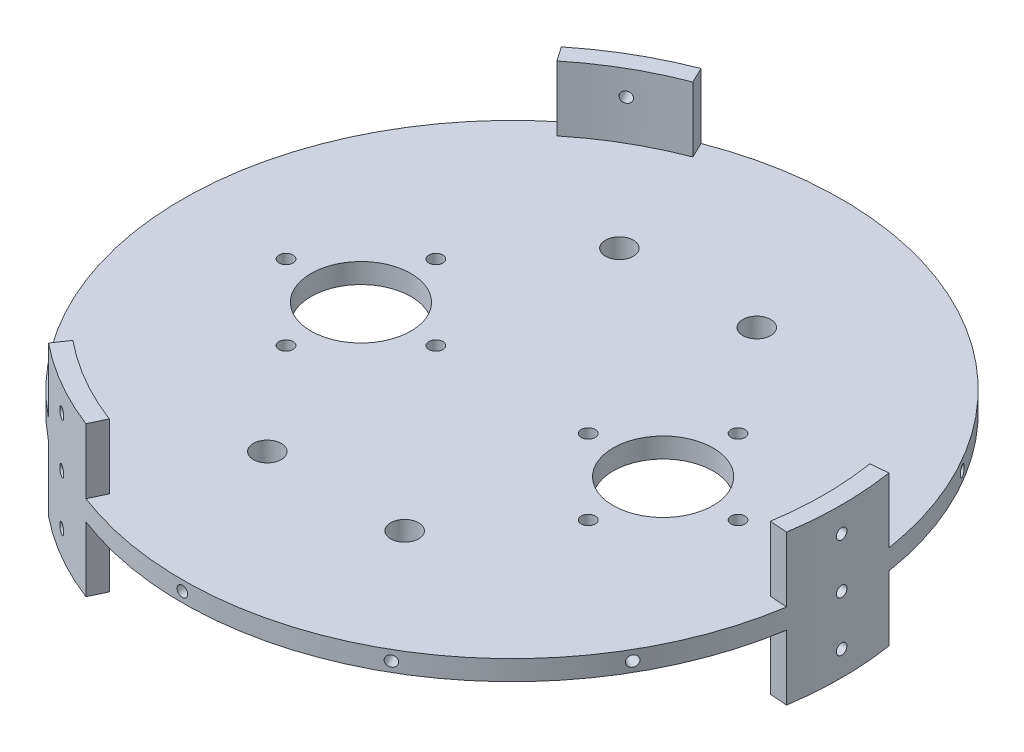
SolidWorks part; units mm, degrees
material "6061-T6 (SS)"
ref_plane "Front" through (0, 0, 0) normal (0, 0, 1) x (1, 0, 0)
ref_plane "Top" through (0, 0, 0) normal (0, 1, 0) x (1, 0, 0)
ref_plane "Right" through (0, 0, 0) normal (1, 0, 0) x (0, 0, -1)
sketch "Sketch1" plane through (0, 0, 0) normal (0, 1, 0) x (1, 0, 0)
  line L1 (0, 0) -> (127.635, 0)
  line L2 (0, 0) -> (0, 127.635)
  line L3 (0, 127.635) -> (127.635, 127.635)
  line L4 (127.635, 0) -> (127.635, 127.635)
  dimension "D1" = 127.635
  dimension "D2" = 127.635
extrude "Main Plate" add sketch "Sketch1" along normal blind 12.7
sketch "Sketch9" plane through (0, 12.7, 0) normal (0, 1, 0) x (1, 0, 0)
  circle A0 centre (63.8175, 63.8175) radius 85.725
  dimension "D1" = 171.45
extrude "Boss-Extrude1" add sketch "Sketch9" against normal up to surface (12.7 mm away) contours A0 up to face at (63.8175, 0, -63.8175)
sketch "Sketch10" plane through (0, 12.7, 0) normal (0, 1, 0) x (1, 0, 0)
  circle A0 centre (63.8175, 63.8175) radius 97.0396
  circle A1 centre (63.8175, 63.8175) radius 83.82
extrude "Cut-Extrude1" cut sketch "Sketch10" against normal blind 167.64 contours A0 | A1
sketch "Sketch14" plane through (0, 12.7, 0) normal (0, 1, 0) x (1, 0, 0)
  line L0 (201.1692, 63.8175) -> (-73.4523, 63.8175) construction
ref_plane "Plane1" through (0, 0, -63.8175) normal (0, 0, -1) x (-1, 0, 0)
ref_plane "Plane3" through (0, 6.35, 0) normal (0, 1, 0) x (1, 0, 0)
ref_plane "Plane2" through (-20.0025, 0, 0) normal (-1, 0, 0) x (0, 0, 1)
sketch "Sketch18" plane through (0, 6.35, 0) normal (0, 1, 0) x (1, 0, 0)
  circle A0 centre (63.8175, 63.8175) radius 83.82
  circle A1 centre (63.8175, 63.8175) radius 79.375
  dimension "D1" = 158.75
extrude "Boss-Extrude2" add sketch "Sketch18" along normal mid plane 38.1
sketch "Sketch15" plane through (-20.0025, 0, 0) normal (-1, 0, 0) x (0, 0, 1)
  line L0 (-63.8175, 87.3125) -> (-63.8175, -87.3125) construction
  line L1 (20.0025, 12.7) -> (-147.6375, 12.7) construction
  line L2 (-147.6375, -12.7) -> (20.0025, -12.7) construction
  line L3 (15.5575, 25.4) -> (-143.1925, 25.4) construction
  circle A0 centre (-63.8175, 6.35) radius 1.3526
  circle A1 centre (-63.8175, 19.05) radius 1.3525
  circle A2 centre (-63.8175, -6.35) radius 1.3526
  dimension "D1" = 2.7051
  dimension "D2" = 6.35
  dimension "D3" = 2.7051
  dimension "D4" = 2.7051
  dimension "D5" = 6.35
  dimension "D6" = 6.35
extrude "Cut-Extrude3" cut sketch "Sketch15" against normal blind 15.24
pattern_circular "CirPattern1" count 12 over 360 about axis through (63.8175, 0, -63.8175) along (0, 1, 0) of "Cut-Extrude3"
sketch "Sketch20" plane through (0, 12.7, 0) normal (0, 1, 0) x (1, 0, 0)
  line L0 (63.8175, 143.1925) -> (63.8175, -15.5575) construction
  line L1 (-15.5575, 63.8175) -> (143.1925, 63.8175) construction
  circle A0 centre (63.8175, 63.8175) radius 79.375 construction
ref_plane "Plane4" through (63.8175, 0, 0) normal (-1, 0, 0) x (0, 0, 1)
sketch "Sketch21" plane through (0, 12.7, 0) normal (0, 1, 0) x (1, 0, 0)
  line L1 (-15.5575, 63.8175) -> (143.1925, 63.8175) construction
  line L2 (102.235, 63.8175) -> (102.235, 100.651) construction
  line L3 (63.8175, 87.3125) -> (63.8175, -87.3125) construction
  circle A0 centre (102.235, 63.8175) radius 12.7
  circle A1 centre (102.235, 82.8675) radius 1.778
  circle A2 centre (25.4, 63.8175) radius 12.7
  circle A3 centre (121.285, 63.8175) radius 1.778
  circle A4 centre (102.235, 44.7675) radius 1.778
  circle A5 centre (83.185, 63.8175) radius 1.778
  circle A6 centre (25.4, 82.8675) radius 1.778
  circle A7 centre (6.35, 63.8175) radius 1.778
  circle A8 centre (25.4, 44.7675) radius 1.778
  circle A9 centre (44.45, 63.8175) radius 1.778
  dimension "D1" = 25.4
  dimension "D2" = 3.556
  dimension "D6" = 19.05
  dimension "D3" = 19.05
  dimension "D4" = 76.835
  dimension "D7" = 19.05
  dimension "D5" = 4
extrude "CO2 Mounts" cut sketch "Sketch21" against normal through all
sketch "Sketch22" plane through (0, 12.7, 0) normal (0, 1, 0) x (1, 0, 0)
  line L0 (63.8175, 87.3125) -> (63.8175, -87.3125) construction
  line L1 (87.3125, 63.8175) -> (-87.3125, 63.8175) construction
  circle A0 centre (46.355, 108.585) radius 3.556
  circle A1 centre (81.28, 108.585) radius 3.556
  circle A2 centre (81.28, 19.05) radius 3.556
  circle A3 centre (46.355, 19.05) radius 3.556
  dimension "D1" = 7.112
  dimension "D2" = 34.925
  dimension "D3" = 89.535
extrude "Cut-Extrude5" cut sketch "Sketch22" against normal through all
sketch "Sketch23" plane through (0, 12.7, 0) normal (0, 1, 0) x (1, 0, 0)
  line L0 (13.6787, 125.352) -> (7.5523, 134.2379)
  line L1 (15.1867, 11.8815) -> (13.6787, 2.283) construction
  line L3 (-15.5575, 63.8175) -> (143.1925, 63.8175) construction
  line L4 (63.8175, 143.1925) -> (63.8175, -15.5575) construction
  line L5 (-15.5575, 63.8175) -> (143.1925, 63.8175)
  line L6 (63.8175, 143.1925) -> (63.8175, -15.5575)
  line L7 (13.6787, 2.283) -> (6.9592, -7.4631)
  line L8 (-19.2671, 125.3206) -> (-48.797, 60.3978)
  line L9 (-48.797, 60.3978) -> (-9.8843, 7.0525)
  line L10 (-9.8843, 7.0525) -> (6.9592, -7.4631)
  line L11 (24.1345, -4.9259) -> (13.6787, 2.283) construction
  line L14 (7.5523, 134.2379) -> (-19.2671, 125.3206)
  line L15 (24.1345, 132.5609) -> (13.6787, 125.352) construction
  line L28 (63.8175, 63.8175) -> (24.1345, -4.9259) construction
  line L29 (63.8175, 63.8175) -> (24.1345, 132.5609) construction
  line L30 (142.1773, 76.4717) -> (152.9359, 77.3344)
  line L31 (152.9359, 77.3344) -> (158.6231, 105.0193)
  line L32 (158.6231, 105.0193) -> (117.1632, 163.0543)
  line L33 (117.1632, 163.0543) -> (51.5085, 156.0277)
  line L34 (51.5085, 156.0277) -> (30.5159, 148.6985)
  line L35 (35.5964, 138.0062) -> (30.5159, 148.6985)
  line L36 (35.5964, -10.3712) -> (30.9643, -20.1198)
  line L37 (30.9643, -20.1198) -> (52.0965, -38.8874)
  line L38 (52.0965, -38.8874) -> (123.0863, -31.9996)
  line L39 (123.0863, -31.9996) -> (149.8284, 28.3723)
  line L40 (149.8284, 28.3723) -> (153.9775, 50.217)
  line L41 (142.1773, 51.1633) -> (153.9775, 50.217)
  circle A0 centre (63.8175, 63.8175) radius 79.375 construction
  arc A1 (13.6787, 2.283) -> (13.6787, 125.352) centre (63.8175, 63.8175) cw
  circle A3 centre (63.8175, 63.8175) radius 79.375
  circle A4 centre (63.8175, 63.8175) radius 79.375
  arc A6 (35.5964, 138.0062) -> (142.1773, 76.4717) centre (63.8175, 63.8175) cw
  arc A7 (142.1773, 51.1633) -> (35.5964, -10.3712) centre (63.8175, 63.8175) cw
  dimension "D1" = 79.375
  dimension "D2" = 0
  dimension "D3" = 12.7
  dimension "D4" = 90
  dimension "D5" = 12.7
  dimension "D6" = 90
  dimension "D8" = 60.004
  dimension "D9" = 60.004
  dimension "D7" = 3
extrude "Cut-Extrude6" cut sketch "Sketch23" along normal up to next (12.7 mm away)
mirror "Mirror1" about plane through (0, 6.35, 0) normal (0, 1, 0) of "Cut-Extrude6"
sketch "Sketch25" plane through (0, 0, 0) normal (0, -1, 0) x (1, 0, 0)
  line L0 (-15.5575, -63.8175) -> (143.1925, -63.8175) construction
  line L1 (63.8175, -143.1925) -> (63.8175, 15.5575) construction
  line L2 (-15.5575, -63.8175) -> (143.1925, -63.8175)
  line L3 (63.8175, -143.1925) -> (63.8175, 15.5575)
  line L4 (63.8175, -143.1925) -> (63.8175, 15.5575)
  line L5 (-15.5575, -63.8175) -> (143.1925, -63.8175)
  line L6 (35.5964, -138.0062) -> (33.6829, -142.0332) construction
  line L7 (13.6787, -125.352) -> (11.148, -129.0227) construction
  line L8 (142.1773, -51.1633) -> (146.6216, -50.8069) construction
  line L9 (146.6216, -76.8281) -> (142.1773, -76.4717) construction
  line L10 (33.6829, 14.3982) -> (35.5964, 10.3712) construction
  line L11 (11.148, 1.3877) -> (13.6787, -2.283) construction
  line L12 (35.5964, -138.0062) -> (33.6829, -142.0332)
  line L13 (13.6787, -125.352) -> (11.148, -129.0227)
  line L14 (142.1773, -51.1633) -> (146.6216, -50.8069)
  line L15 (146.6216, -76.8281) -> (142.1773, -76.4717)
  line L16 (33.6829, 14.3982) -> (35.5964, 10.3712)
  line L17 (11.148, 1.3877) -> (13.6787, -2.283)
  circle A0 centre (46.355, -19.05) radius 6.35
  circle A1 centre (81.28, -19.05) radius 6.35
  circle A2 centre (81.28, -108.585) radius 6.35
  circle A3 centre (46.355, -108.585) radius 6.35
  arc A4 (13.6787, -125.352) -> (35.5964, -138.0062) centre (63.8175, -63.8175) ccw construction
  arc A5 (142.1773, -76.4717) -> (142.1773, -51.1633) centre (63.8175, -63.8175) ccw construction
  arc A6 (35.5964, 10.3712) -> (13.6787, -2.283) centre (63.8175, -63.8175) ccw construction
  arc A7 (146.6216, -50.8069) -> (33.6829, 14.3982) centre (63.8175, -63.8175) ccw construction
  arc A8 (33.6829, -142.0332) -> (146.6216, -76.8281) centre (63.8175, -63.8175) ccw construction
  arc A9 (11.148, 1.3877) -> (11.148, -129.0227) centre (63.8175, -63.8175) ccw construction
  arc A10 (13.6787, -125.352) -> (35.5964, -138.0062) centre (63.8175, -63.8175) ccw
  arc A11 (142.1773, -76.4717) -> (142.1773, -51.1633) centre (63.8175, -63.8175) ccw
  arc A12 (35.5964, 10.3712) -> (13.6787, -2.283) centre (63.8175, -63.8175) ccw
  arc A13 (146.6216, -50.8069) -> (33.6829, 14.3982) centre (63.8175, -63.8175) ccw
  arc A14 (33.6829, -142.0332) -> (146.6216, -76.8281) centre (63.8175, -63.8175) ccw
  arc A15 (11.148, 1.3877) -> (11.148, -129.0227) centre (63.8175, -63.8175) ccw
  dimension "D1" = 12.7
extrude "used to vary plate width in desin study" cut sketch "Sketch25" against normal blind 3.81 contours L12 A14 L15 A11 L14 A13 L16 A12 L17 A15 L13 A10
mirror "Mirror of previous cut" about plane through (0, 6.35, 0) normal (0, 1, 0) of "used to vary plate width in desin study"
